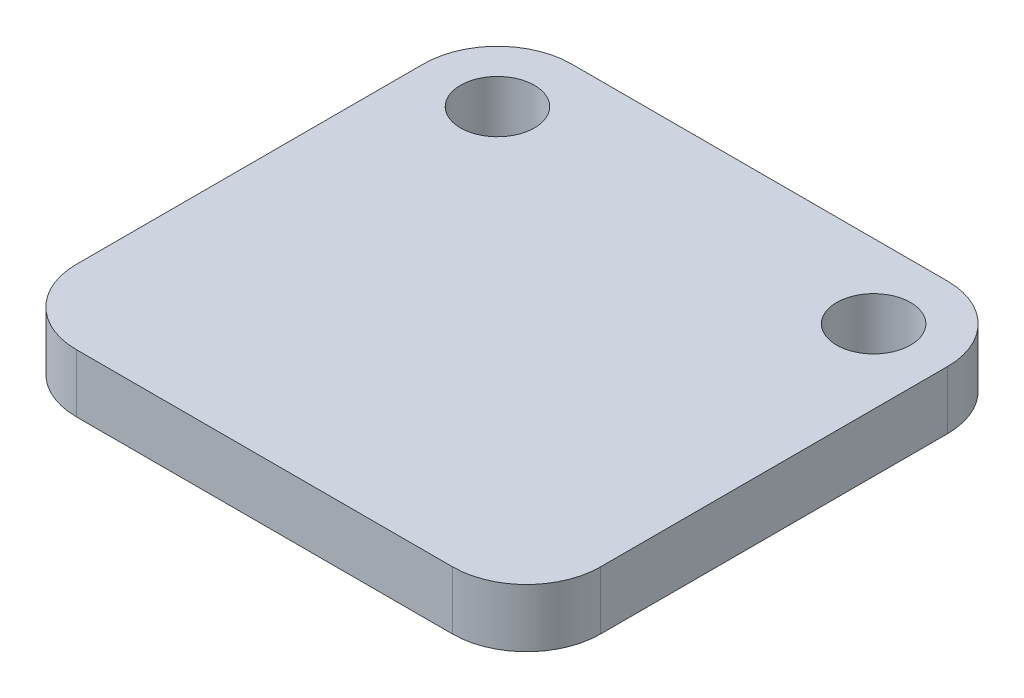
SolidWorks part; units mm, degrees
ref_plane "Front Plane" through (0, 0, 0) normal (0, 0, 1) x (1, 0, 0)
ref_plane "Top Plane" through (0, 0, 0) normal (0, 1, 0) x (1, 0, 0)
ref_plane "Right Plane" through (0, 0, 0) normal (1, 0, 0) x (0, 0, -1)
sketch "Sketch1" plane through (0, 0, 0) normal (0, 1, 0) x (1, 0, 0)
  line L1 (0, 0) -> (18, 0)
  line L2 (0, 0) -> (0, 17)
  line L3 (0, 17) -> (18, 17)
  line L4 (18, 0) -> (18, 17)
  dimension "D1" = 18
  dimension "D2" = 17
extrude "Boss-Extrude1" add sketch "Sketch1" along normal blind 2
sketch "Sketch2" plane through (0, 2, 0) normal (0, 1, 0) x (1, 0, 0)
  line L0 (18, 17) -> (0, 17) construction
  line L1 (0, 17) -> (0, 0) construction
  line L2 (9, 17) -> (9, 0) construction
  line L3 (0, 0) -> (18, 0) construction
  circle A0 centre (2.54, 14.46) radius 1.27
  circle A1 centre (15.46, 14.46) radius 1.27
  point P10 (15.46, 14.46)
  dimension "D1" = 2.54
  dimension "D2" = 2.54
  dimension "D3" = 2.54
extrude "Cut-Extrude1" cut sketch "Sketch2" against normal through all
fillet "Fillet1" radius 2.54 4 edges at (18, 1, 0) (0, 1, 0) (18, 1, -17) (0, 1, -17)
